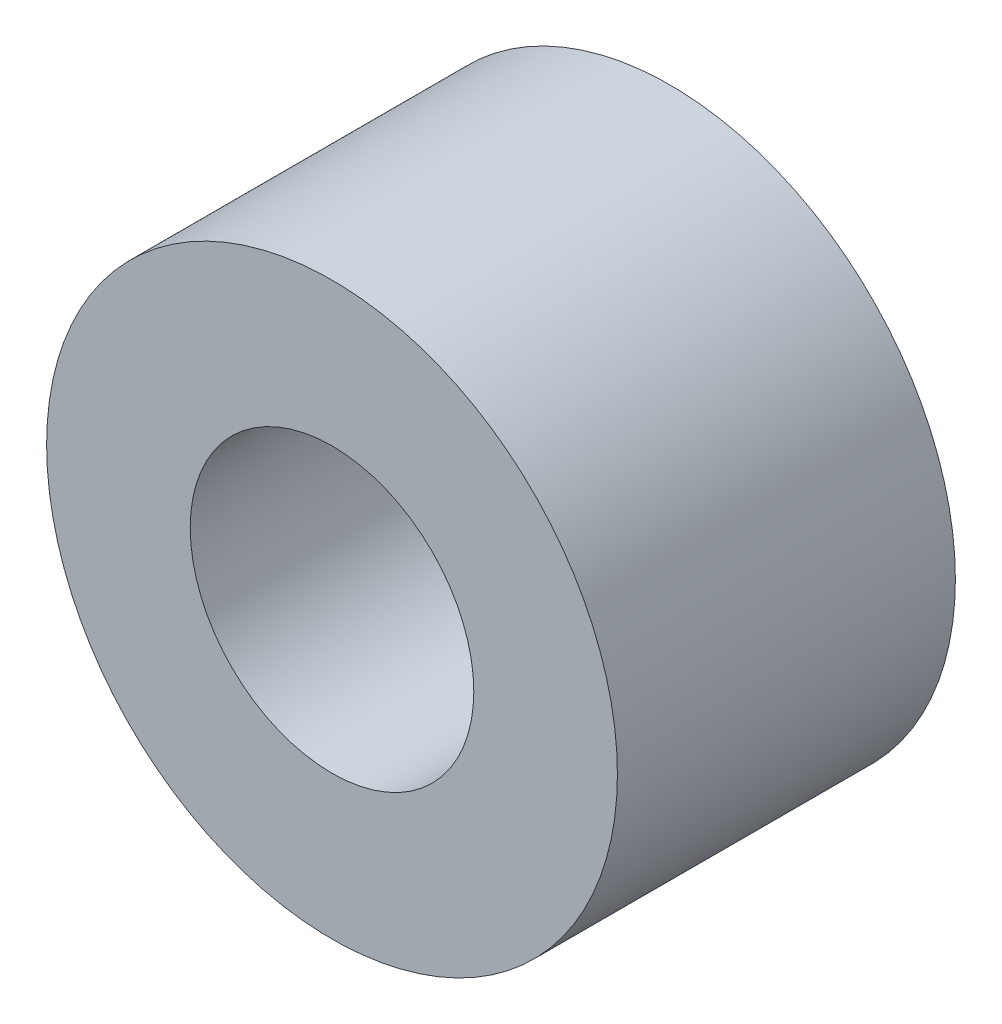
SolidWorks part; units mm, degrees
ref_plane "Front Plane" through (0, 0, 0) normal (0, 0, 1) x (1, 0, 0)
ref_plane "Top Plane" through (0, 0, 0) normal (0, 1, 0) x (1, 0, 0)
ref_plane "Right Plane" through (0, 0, 0) normal (1, 0, 0) x (0, 0, -1)
sketch "Sketch1" plane through (0, 0, 0) normal (0, 0, 1) x (1, 0, 0)
  circle A0 centre (0, 0) radius 15.2
  circle A1 centre (0, 0) radius 7.5513
  dimension "D1" = 30.4
  dimension "D2" = 15.1026
extrude "Boss-Extrude1" add sketch "Sketch1" along normal blind 18
